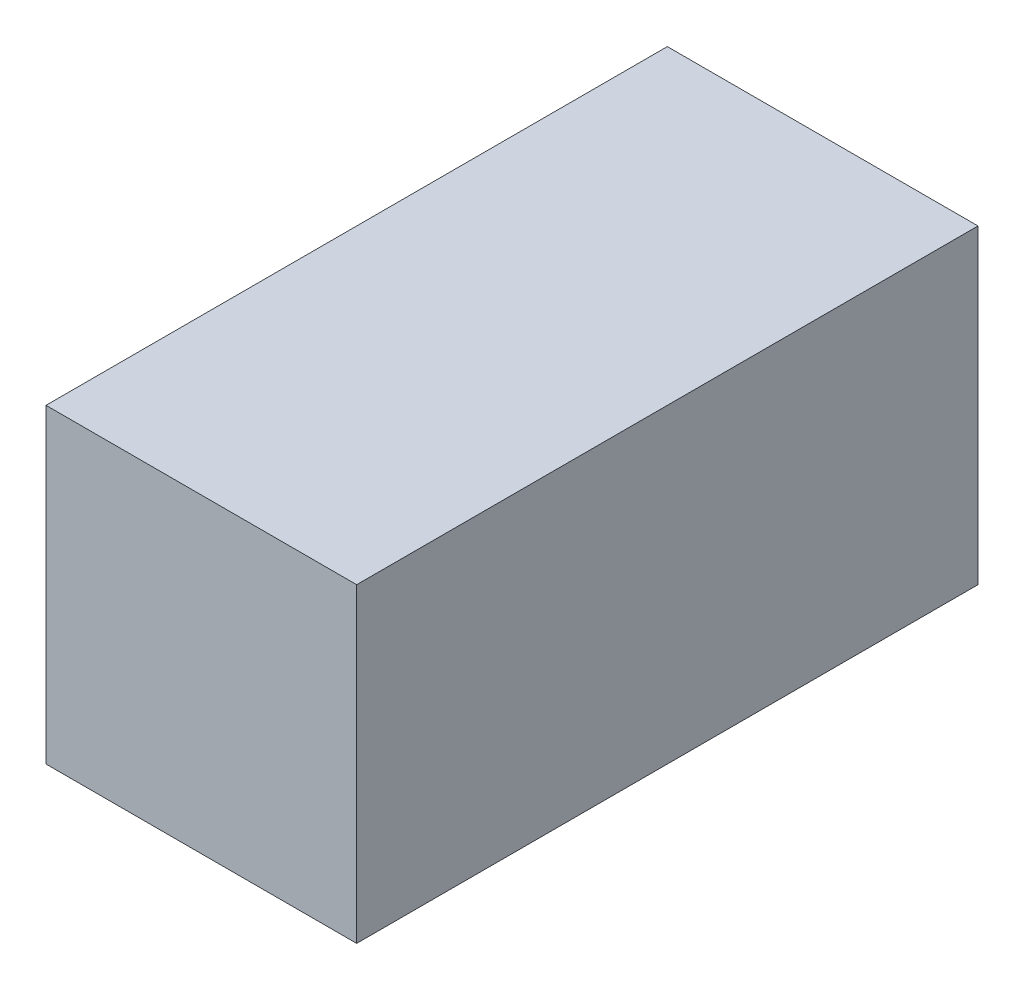
SolidWorks part; units mm, degrees
ref_plane "Alzado" through (0, 0, 0) normal (0, 0, 1) x (1, 0, 0)
ref_plane "Planta" through (0, 0, 0) normal (0, 1, 0) x (1, 0, 0)
ref_plane "Vista lateral" through (0, 0, 0) normal (1, 0, 0) x (0, 0, -1)
sketch "Croquis1" plane through (0, 0, 0) normal (0, 0, 1) x (1, 0, 0)
  line L1 (-250, -250) -> (250, -250)
  line L2 (-250, -250) -> (-250, 250)
  line L3 (-250, 250) -> (250, 250)
  line L4 (250, -250) -> (250, 250)
  line L5 (-250, -250) -> (250, 250) construction
  line L6 (-250, 250) -> (250, -250) construction
  point P0 (0, 0)
  dimension "D1" = 500
  dimension "D2" = 500
extrude "Saliente-Extruir1" add sketch "Croquis1" along normal blind 1000
